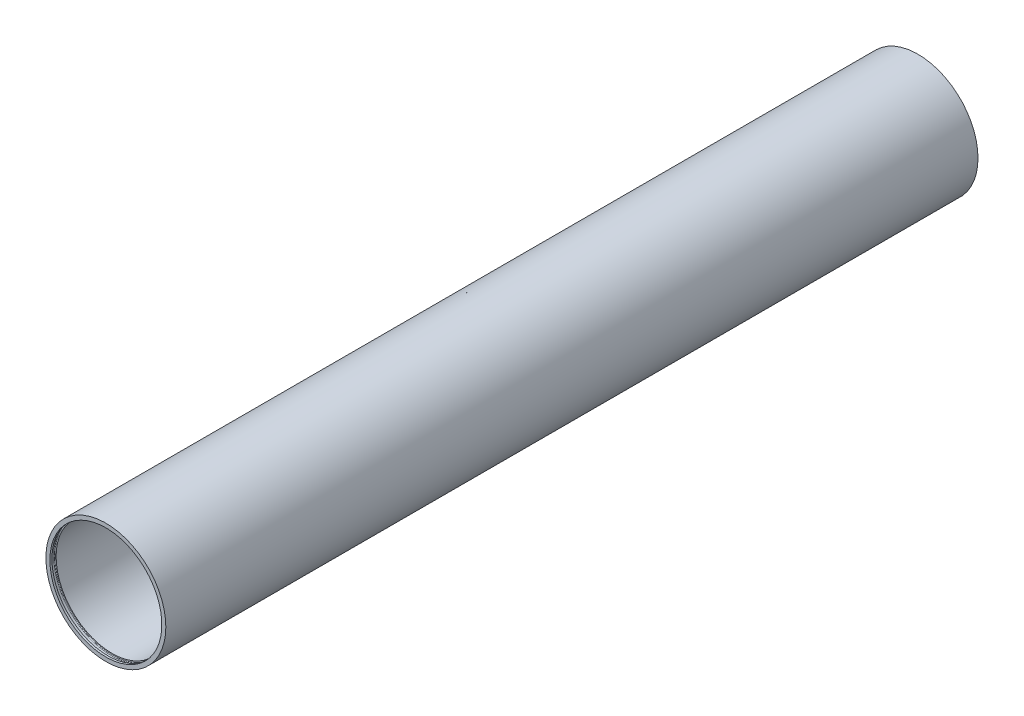
SolidWorks part; units mm, degrees
material "6061-T6 (SS)"
ref_plane "Bottom" through (0, 0, 0) normal (0, 0, 1) x (1, 0, 0)
ref_plane "Centerline" through (0, 0, 0) normal (0, 1, 0) x (1, 0, 0)
ref_plane "Front" through (0, 0, 0) normal (1, 0, 0) x (0, 0, -1)
sketch "Sketch1" plane through (0, 0, 0) normal (0, 0, 1) x (1, 0, 0)
  circle A0 centre (0, 0) radius 37.5
  dimension "D1" = 75
extrude "Boss-Extrude1" add sketch "Sketch1" along normal blind 507.84
ref_plane "Plane1" through (0, 0, 0) normal (0, 0, -1) x (-1, 0, 0)
sketch "Sketch3" plane through (0, 0, 0) normal (0, 0, -1) x (-1, 0, 0)
  circle A0 centre (0, 0) radius 35
extrude "Cut-Extrude1" cut sketch "Sketch3" against normal blind 507.84
ref_plane "Plane2" through (0, 0, 507.84) normal (0, 0, 1) x (1, 0, 0)
ref_plane "Plane4" through (0, 0, 1.27) normal (0, 0, 1) x (1, 0, 0)
ref_plane "Plane9" through (0, 0, 506.57) normal (0, 0, 1) x (1, 0, 0)
sketch "Sketch5" plane through (0, 0, 1.27) normal (0, 0, 1) x (1, 0, 0)
  circle A0 centre (0, 0) radius 37.5
ref_plane "Plane5" through (0, 0, 507.84) normal (-1, 0, 0) x (0, 1, 0)
sketch "Sketch7" plane through (0, 0, 507.84) normal (-1, 0, 0) x (0, 1, 0)
  line L0 (35.7, 490.1102) -> (31.5, 490.1102)
  line L1 (31.5, 490.1102) -> (31.5, 492.6602)
  line L2 (31.5, 492.6602) -> (35.7, 492.6602)
  line L3 (36.1, 492.2602) -> (36.1, 490.5102)
  line L4 (0, -50) -> (0, 50) construction
  arc A0 (36.1, 490.5102) -> (35.7, 490.1102) centre (35.7, 490.5102) cw
  arc A1 (36.1, 492.2602) -> (35.7, 492.6602) centre (35.7, 492.2602) ccw
  dimension "D1" = 0.4
  dimension "D2" = 0.4
ref_plane "Plane6" through (0, 0, 507.84) normal (-1, 0, 0) x (0, 1, 0)
sketch "Sketch9" plane through (0, 0, 507.84) normal (-1, 0, 0) x (0, 1, 0)
  line L0 (35.7, 503.96) -> (31.5, 503.96)
  line L1 (31.5, 503.96) -> (31.5, 506.57)
  line L2 (31.5, 506.57) -> (35.7, 506.57)
  line L3 (36.1, 506.17) -> (36.1, 504.36)
  line L4 (0, -50) -> (0, 50) construction
  line L5 (-41.25, 506.57) -> (41.25, 506.57) construction
  arc A0 (36.1, 504.36) -> (35.7, 503.96) centre (35.7, 504.36) cw
  arc A1 (36.1, 506.17) -> (35.7, 506.57) centre (35.7, 506.17) ccw
  dimension "D1" = 0.4
  dimension "D2" = 0.4
  dimension "D3" = 0
  dimension "D4" = 2.61
revolve "Groove for ANSI B27.7 - 3BM1-68, Basic Internal Retaining Ring1" cut sketch "Sketch9"
ref_plane "Plane7" through (0, 0, 507.84) normal (-1, 0, 0) x (0, 1, 0)
sketch "Sketch11" plane through (0, 0, 507.84) normal (-1, 0, 0) x (0, 1, 0)
  line L0 (35.7, 1.27) -> (31.5, 1.27)
  line L1 (31.5, 1.27) -> (31.5, 3.88)
  line L2 (31.5, 3.88) -> (35.7, 3.88)
  line L3 (36.1, 3.48) -> (36.1, 1.67)
  line L4 (0, -50) -> (0, 50) construction
  line L5 (-38.5, 1.27) -> (38.5, 1.27) construction
  arc A0 (36.1, 1.67) -> (35.7, 1.27) centre (35.7, 1.67) cw
  arc A1 (36.1, 3.48) -> (35.7, 3.88) centre (35.7, 3.48) ccw
  dimension "D1" = 0.4
  dimension "D2" = 0.4
  dimension "D3" = 0
revolve "Groove for ANSI B27.7 - 3BM1-68, Basic Internal Retaining Ring2" cut sketch "Sketch11" angle 360 about L4
